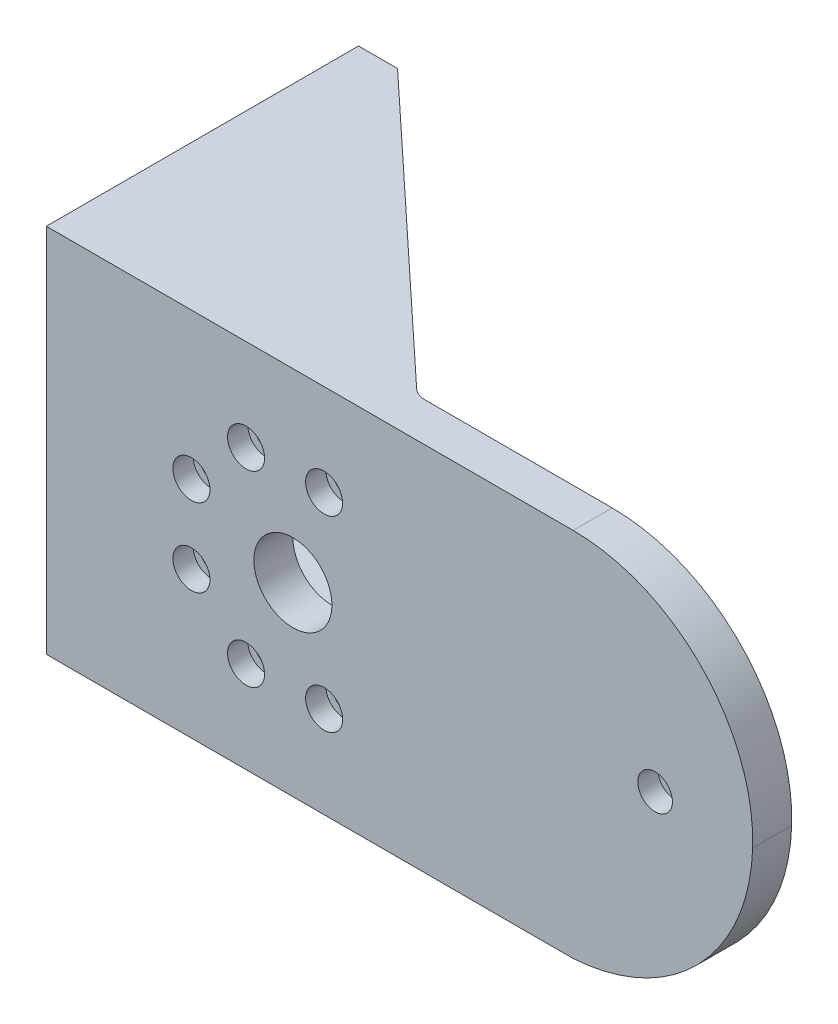
SolidWorks part; units mm, degrees
ref_plane "Front Plane" through (0, 0, 0) normal (0, 0, 1) x (1, 0, 0)
ref_plane "Top Plane" through (0, 0, 0) normal (0, 1, 0) x (1, 0, 0)
ref_plane "Right Plane" through (0, 0, 0) normal (1, 0, 0) x (0, 0, -1)
sketch "Sketch3" plane through (0, 0, 0) normal (0, 0, 1) x (1, 0, 0)
  line L0 (163.6171, 80.0599) -> (203.6171, 80.0599)
  line L6 (68.6171, 80.0599) -> (163.6171, 80.0599)
  line L10 (68.6171, 80.0599) -> (68.6171, -14.9401)
  line L36 (-101.4371, 49.8561) -> (-17.2351, 49.8561) construction
  line L61 (163.6171, -14.9401) -> (203.6171, -14.9401)
  line L62 (249.6171, 80.0599) -> (249.6171, -14.9401) construction
  line L64 (147.7099, 80.0599) -> (147.7099, -14.9401) construction
  line L70 (68.6171, -14.9401) -> (163.6171, -14.9401)
  circle A22 centre (163.6171, 32.5599) radius 10 construction
  circle A23 centre (189.6171, 42.5599) radius 2.75 construction
  circle A24 centre (155.6171, 56.5599) radius 2.75 construction
  circle A25 centre (175.6171, 56.5599) radius 2.75 construction
  circle A26 centre (155.6171, 8.5599) radius 2.75 construction
  circle A27 centre (175.6171, 8.5599) radius 2.75 construction
  circle A28 centre (189.6171, 22.5599) radius 2.75 construction
  circle A31 centre (224.6171, 32.5599) radius 2.921
  arc A32 (203.6171, 80.0599) -> (249.6171, 32.5599) centre (203.6171, 34.0362) cw
  arc A33 (249.6171, 32.5599) -> (203.6171, -14.9401) centre (200.4637, 34.1375) cw
  circle A40 centre (131.8026, 32.5599) radius 10
  circle A41 centre (139.8026, 8.5599) radius 2.75
  circle A42 centre (119.8026, 8.5599) radius 2.75
  circle A43 centre (105.8026, 22.5599) radius 2.75
  circle A44 centre (105.8026, 42.5599) radius 2.75
  circle A45 centre (119.8026, 56.5599) radius 2.75
  circle A46 centre (139.8026, 56.5599) radius 2.75
  point P23 (203.6171, 80.0599)
  dimension "D3" = 10
  dimension "D4" = 26
  dimension "D7" = 5.5
  dimension "D21" = 135
  dimension "D23" = 47.5
  dimension "D1" = 20
  dimension "D5" = 5.842
  dimension "D6" = 35
  dimension "D8" = 25
  dimension "D10" = 8
  dimension "D11" = 24
  dimension "D12" = 20
  dimension "D15" = 20
  dimension "D16" = 8
  dimension "D17" = 20
  dimension "D18" = 48
  dimension "D19" = 48
  dimension "D20" = 95
  dimension "D13" = 26
  dimension "D14" = 24
extrude "Boss-Extrude1" add sketch "Sketch3" along normal blind 10
sketch "Sketch4" plane through (0, 0, 0) normal (0, 0, -1) x (-1, 0, 0)
  line L0 (-68.6171, -14.9401) -> (-203.6171, -14.9401) construction
  line L1 (-68.6171, 80.0599) -> (-78.6171, 80.0599)
  line L2 (-68.6171, 80.0599) -> (-68.6171, -14.9401)
  line L3 (-68.6171, -14.9401) -> (-78.6171, -14.9401)
  line L4 (-78.6171, 80.0599) -> (-78.6171, -14.9401)
  dimension "D1" = 10
extrude "Boss-Extrude2" add sketch "Sketch4" along normal blind 70
sketch "Sketch8" plane through (68.6171, 0, 0) normal (-1, 0, 0) x (0, 0, 1)
  line L0 (10, 80.0599) -> (-70, 80.0599) construction
  line L1 (-40, 32.5599) -> (-56.1679, 25.863) construction
  line L2 (-70, 32.5599) -> (0, 32.5599) construction
  line L3 (-70, -14.9401) -> (-70, 80.0599) construction
  circle A0 centre (-40, 32.5599) radius 10
  circle A1 centre (-56.1679, 25.863) radius 2.75
  circle A2 centre (-56.1679, 39.2569) radius 2.75
  circle A3 centre (-46.697, 48.7278) radius 2.75
  circle A4 centre (-33.303, 48.7278) radius 2.75
  circle A5 centre (-23.8321, 39.2569) radius 2.75
  circle A6 centre (-23.8321, 25.863) radius 2.75
  circle A7 centre (-33.303, 16.392) radius 2.75
  circle A8 centre (-46.697, 16.392) radius 2.75
  point P27 (-40, 32.5599)
  dimension "D1" = 20
  dimension "D6" = 5.5
  dimension "D2" = 47.5
  dimension "D3" = 30
  dimension "D4" = 17.5
  dimension "D5" = 22.5
  dimension "D7" = 8
extrude "Cut-Extrude2" cut sketch "Sketch8" against normal blind 43.8
sketch "Sketch9" plane through (0, -14.9401, 0) normal (0, -1, 0) x (1, 0, 0)
  line L0 (78.6171, -70) -> (153.6171, 0)
  line L1 (55, 0) -> (-55, 0) construction
  line L2 (78.6171, 0) -> (203.6171, 0) construction
  line L3 (78.6171, -70) -> (78.6171, 0)
  line L4 (78.6171, 0) -> (153.6171, 0)
extrude "Boss-Extrude3" add sketch "Sketch9" against normal blind 7.5
ref_plane "Plane1" through (0, 32.5599, 0) normal (0, -1, 0) x (-1, 0, 0)
mirror "Mirror1" about plane through (0, 32.5599, 0) normal (0, -1, 0) of "Boss-Extrude3"
fillet "Fillet1" radius 5 2 edges at (153.6171, 76.3099, 0) (153.6171, -11.1901, 0)
sketch "Sketch11" plane through (0, 0, 0) normal (0, 0, -1) x (-1, 0, 0)
  line L0 (-78.6171, 72.5599) -> (-78.6171, -7.4401) construction
  line L1 (-91.1171, -2.4401) -> (-116.1171, -2.4401)
  line L2 (-91.1171, -2.4401) -> (-91.1171, 22.5599)
  line L3 (-91.1171, 22.5599) -> (-116.1171, 22.5599)
  line L4 (-116.1171, -2.4401) -> (-116.1171, 22.5599)
  line L5 (-155.5879, -7.4401) -> (-78.6171, -7.4401) construction
  dimension "D1" = 12.5
  dimension "D2" = 25
  dimension "D3" = 25
  dimension "D4" = 5
extrude "Cut-Extrude3" [suppressed] cut sketch "Sketch11" against normal through all
fillet "Fillet3" [suppressed] radius 3
sketch "Sketch14" plane through (0, 0, 10) normal (0, 0, 1) x (1, 0, 0)
  circle A0 centre (119.8026, 56.5599) radius 4.75
  circle A1 centre (139.8026, 56.5599) radius 4.75
  circle A2 centre (105.8026, 42.5599) radius 4.75
  circle A3 centre (119.8026, 8.5599) radius 4.75
  circle A4 centre (139.8026, 8.5599) radius 4.75
  circle A5 centre (105.8026, 22.5599) radius 4.75
  circle A6 centre (224.6171, 32.5599) radius 4.445
  dimension "D1" = 9.5
  dimension "D2" = 8.89
extrude "Cut-Extrude4" cut sketch "Sketch14" against normal blind 5.2
sketch "Sketch15" plane through (78.6171, 0, 0) normal (1, 0, 0) x (0, 0, -1)
  circle A0 centre (23.8321, 39.2569) radius 4.75
  circle A1 centre (33.303, 48.7278) radius 4.75
  circle A2 centre (46.697, 48.7278) radius 4.75
  circle A3 centre (56.1679, 39.2569) radius 4.75
  circle A4 centre (56.1679, 25.863) radius 4.75
  circle A5 centre (46.697, 16.392) radius 4.75
  circle A6 centre (33.303, 16.392) radius 4.75
  circle A7 centre (23.8321, 25.863) radius 4.75
  dimension "D1" = 9.5
extrude "Cut-Extrude5" cut sketch "Sketch15" against normal blind 5.3
